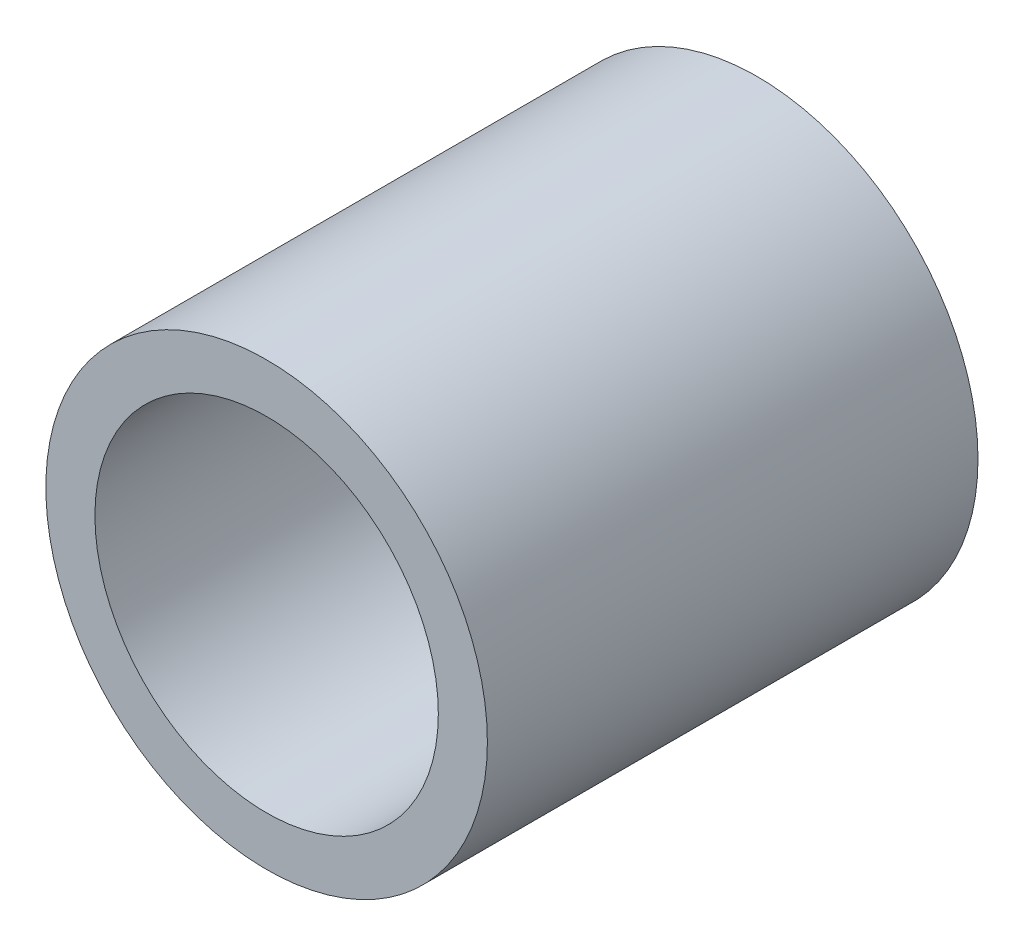
SolidWorks part; units mm, degrees
ref_plane "Front Plane" through (0, 0, 0) normal (0, 0, 1) x (1, 0, 0)
ref_plane "Top Plane" through (0, 0, 0) normal (0, 1, 0) x (1, 0, 0)
ref_plane "Right Plane" through (0, 0, 0) normal (1, 0, 0) x (0, 0, -1)
sketch "Sketch1" plane through (0, 0, 0) normal (0, 0, 1) x (1, 0, 0)
  circle A0 centre (0, 0) radius 14.2875
  circle A1 centre (0, 0) radius 11.1125
  dimension "D1" = 28.575
  dimension "ID" = 22.225
extrude "Extrude1" add sketch "Sketch1" along normal mid plane 31.75
sketch "Sketch2" plane through (0, 0, 0) normal (1, 0, 0) x (0, 0, -1)
  line L0 (-15.875, -11.1125) -> (15.875, -11.1125) construction
  line L3 (15.875, 11.1125) -> (-15.875, 11.1125) construction
  line L5 (-15.875, -11.1125) -> (15.875, -11.1125)
  line L6 (15.875, 11.1125) -> (-15.875, 11.1125)
sketch "Sketch4" plane through (0, 0, 15.875) normal (0, 0, 1) x (1, 0, 0)
  line L0 (0, 0) -> (-7.8577, 7.8577)
  line L1 (0, -48.895) -> (0, 48.895) construction
  circle A0 centre (0, 0) radius 11.1125 construction
  dimension "D1" = 45
